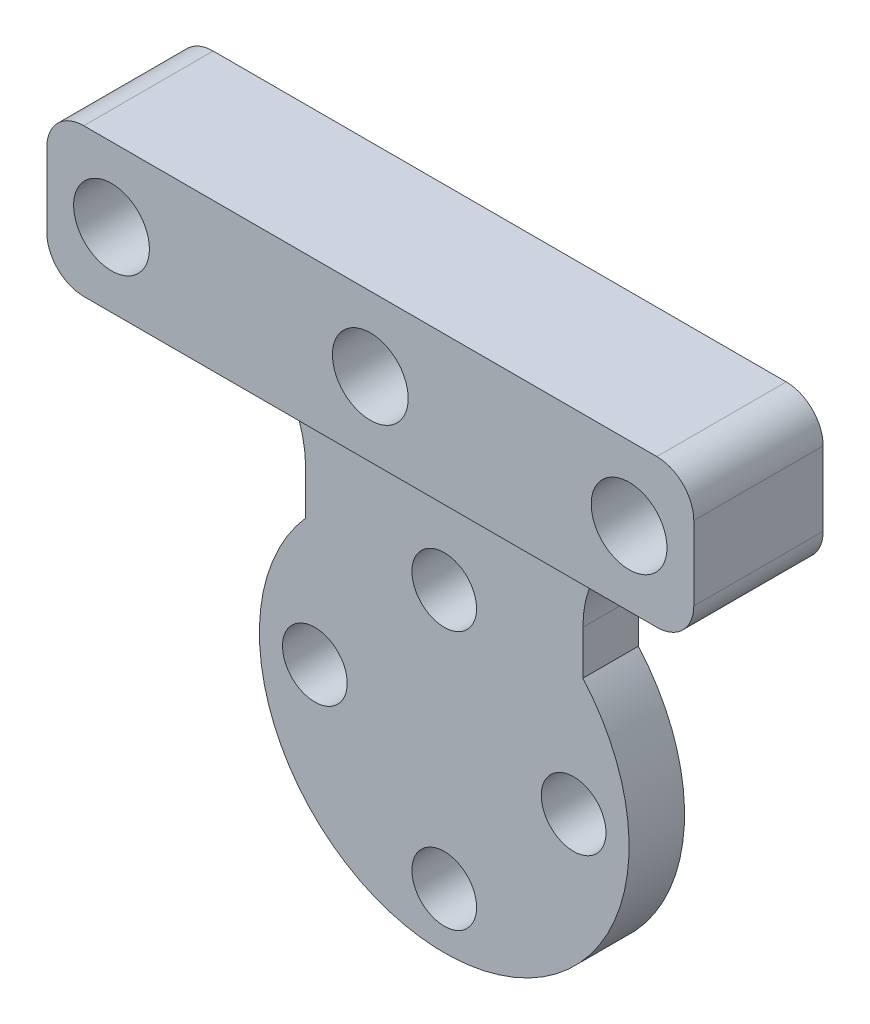
SolidWorks part; units mm, degrees
ref_plane "Спереди" through (0, 0, 0) normal (0, 0, 1) x (1, 0, 0)
ref_plane "Сверху" through (0, 0, 0) normal (0, 1, 0) x (1, 0, 0)
ref_plane "Справа" through (0, 0, 0) normal (1, 0, 0) x (0, 0, -1)
other "Configuration Table"
sketch "Эскиз1" plane through (0, 0, 0) normal (0, 0, 1) x (1, 0, 0)
  circle A0 centre (0, 0) radius 10
  circle A1 centre (0, 0) radius 7 construction
  circle A2 centre (-7, 0) radius 1.75
  circle A3 centre (0, 7) radius 1.75
  circle A4 centre (7, 0) radius 1.75
  circle A5 centre (0, -7) radius 1.75
  dimension "D1" = 20
  dimension "D2" = 14
  dimension "D3" = 3.5
extrude "Бобышка-Вытянуть1" add sketch "Эскиз1" along normal blind 3
sketch "Эскиз6" plane through (0, 0, 3) normal (0, 0, 1) x (1, 0, 0)
  line L0 (0, -1000) -> (0, 49000) construction
  line L1 (-7.5, 6.6144) -> (-7.5, 15)
  line L2 (-7.5, 15) -> (-17.5, 15)
  line L3 (-17.5, 15) -> (-17.5, 23)
  line L4 (-17.5, 23) -> (17.5, 23)
  line L5 (17.5, 15) -> (17.5, 23)
  line L6 (7.5, 15) -> (17.5, 15)
  line L7 (7.5, 6.6144) -> (7.5, 15)
  circle A0 centre (0, 0) radius 10
  circle A1 centre (0, 0) radius 10 construction
  point P13 (0, 23)
  circle M12 centre (0, 0) radius 10
  dimension "D1" = 15
  dimension "D2" = 15
  dimension "D3" = 8
  dimension "D4" = 35
extrude "Бобышка-Вытянуть2" add sketch "Эскиз6" against normal up to surface (3 mm away) contours A0 L0 L4 L3 L2 L1 | L0 L7 L6 L5 L4 M12
sketch "Эскиз7" plane through (0, 0, 3) normal (0, 0, 1) x (1, 0, 0)
  line L1 (-17.5, 23) -> (17.5, 23)
  line L2 (-17.5, 23) -> (-17.5, 15)
  line L3 (-17.5, 15) -> (17.5, 15)
  line L4 (17.5, 23) -> (17.5, 15)
extrude "Бобышка-Вытянуть3" add sketch "Эскиз7" along normal blind 4
fillet "Скругление1" radius 6 2 edges at (-7.5, 15, 1.5) (7.5, 15, 1.5)
sketch "Эскиз8" plane through (0, 0, 7) normal (0, 0, 1) x (1, 0, 0)
  line L0 (-17.5, 19) -> (17.5, 19) construction
  line L1 (-17.5, 23) -> (-17.5, 15) construction
  line L2 (17.5, 15) -> (17.5, 23) construction
  circle A0 centre (0, 19) radius 1.75
  circle A1 centre (-14, 19) radius 1.75
  circle A2 centre (14, 19) radius 1.75
  dimension "D1" = 3.5
  dimension "D2" = 14
  dimension "D3" = 14
extrude "Вырез-Вытянуть2" cut sketch "Эскиз8" against normal through all
fillet "Скругление2" radius 2 4 edges at (-17.5, 15, 3.5) (-17.5, 23, 3.5) (17.5, 23, 3.5) (17.5, 15, 3.5)
sketch "Эскиз10" plane through (0, 0, 7) normal (0, 0, 1) x (1, 0, 0)
  circle A0 centre (-14, 19) radius 2.05
  circle A1 centre (0, 19) radius 2.05
  circle A2 centre (14, 19) radius 2.05
  dimension "D1" = 4.1
extrude "Вырез-Вытянуть3" cut sketch "Эскиз10" against normal blind 6
